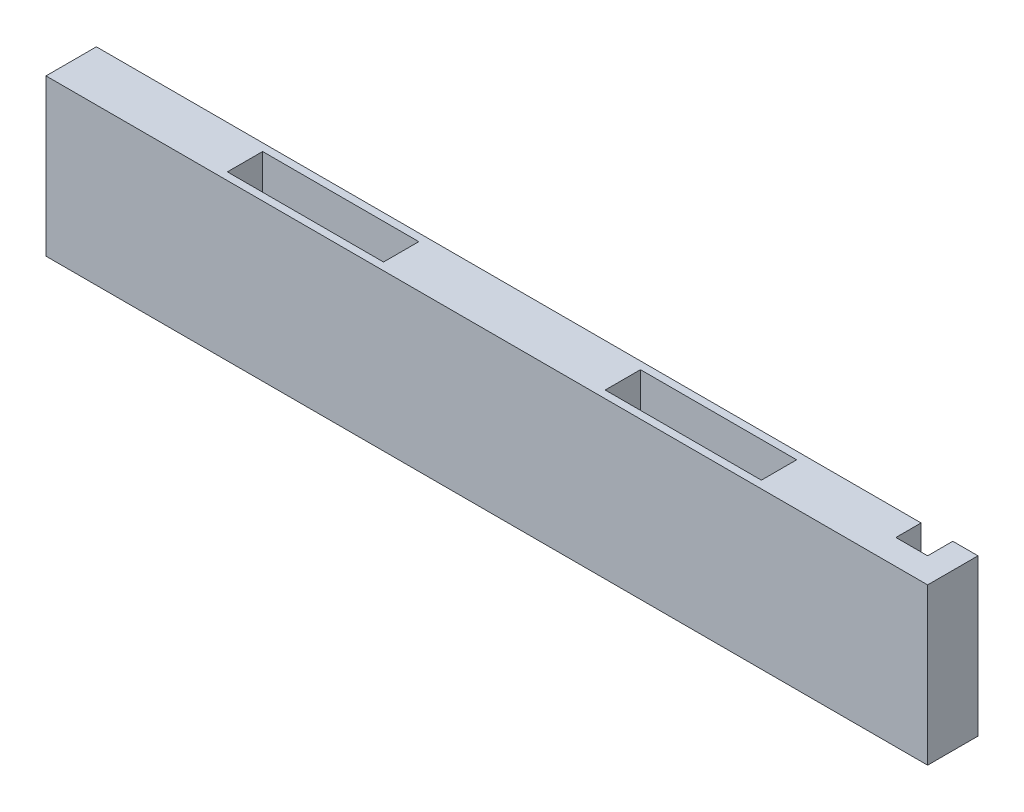
SolidWorks part; units mm, degrees
material "ABS"
ref_plane "Plano frontal" through (0, 0, 0) normal (0, 0, 1) x (1, 0, 0)
ref_plane "Plano superior" through (0, 0, 0) normal (0, 1, 0) x (1, 0, 0)
ref_plane "Plano direito" through (0, 0, 0) normal (1, 0, 0) x (0, 0, -1)
sketch "Esboço1" plane through (0, 0, 0) normal (0, 0, 1) x (1, 0, 0)
  line L1 (87.5, -15.5) -> (-87.5, -15.5)
  line L2 (87.5, -15.5) -> (87.5, 15.5)
  line L3 (87.5, 15.5) -> (-87.5, 15.5)
  line L4 (-87.5, -15.5) -> (-87.5, 15.5)
  line L5 (87.5, -15.5) -> (-87.5, 15.5) construction
  line L6 (87.5, 15.5) -> (-87.5, -15.5) construction
  point P0 (0, 0)
  dimension "D1" = 175
  dimension "D2" = 31
extrude "Ressalto-extrusão1" add sketch "Esboço1" along normal blind 10
sketch "Esboço2" plane through (0, 15.5, 0) normal (0, 1, 0) x (1, 0, 0)
  line L0 (-111.1236, -5) -> (103.3487, -5) construction
  line L1 (0, 16.6179) -> (0, -31.1724) construction
  line L2 (87.5, 0) -> (-87.5, 0) construction
  line L3 (-87.5, -10) -> (-87.5, 0) construction
  line L4 (-22, -8.5) -> (-53, -8.5)
  line L5 (-22, -8.5) -> (-22, -1.5)
  line L6 (-22, -1.5) -> (-53, -1.5)
  line L7 (-53, -8.5) -> (-53, -1.5)
  line L8 (-22, -8.5) -> (-53, -1.5) construction
  line L9 (-22, -1.5) -> (-53, -8.5) construction
  line L10 (22, -1.5) -> (53, -8.5) construction
  line L11 (22, -8.5) -> (53, -1.5) construction
  line L12 (53, -8.5) -> (53, -1.5)
  line L13 (22, -1.5) -> (53, -1.5)
  line L14 (22, -8.5) -> (22, -1.5)
  line L15 (22, -8.5) -> (53, -8.5)
  point P7 (-37.5, -5)
  point P21 (37.5, -5)
  dimension "D1" = 5
  dimension "D2" = 7
  dimension "D3" = 31
  dimension "D4" = 50
extrude "Corte-extrusão1" cut sketch "Esboço2" against normal blind 10.5
sketch "Esboço3" plane through (0, -15.5, 0) normal (0, -1, 0) x (1, 0, 0)
  line L0 (-105.0554, 5) -> (100.316, 5) construction
  line L1 (-87.5, 10) -> (87.5, 10) construction
  line L2 (0, 21.6875) -> (0, -29.1463) construction
  line L3 (-87.5, 10) -> (-87.5, 0) construction
  line L4 (-22, 1.5) -> (-53, 1.5)
  line L5 (-22, 1.5) -> (-22, 8.5)
  line L6 (-22, 8.5) -> (-53, 8.5)
  line L7 (-53, 1.5) -> (-53, 8.5)
  line L8 (-22, 1.5) -> (-53, 8.5) construction
  line L9 (-22, 8.5) -> (-53, 1.5) construction
  line L10 (22, 8.5) -> (53, 1.5) construction
  line L11 (22, 1.5) -> (53, 8.5) construction
  line L12 (53, 1.5) -> (53, 8.5)
  line L13 (22, 8.5) -> (53, 8.5)
  line L14 (22, 1.5) -> (22, 8.5)
  line L15 (22, 1.5) -> (53, 1.5)
  point P6 (-37.5, 5)
  point P19 (37.5, 5)
  dimension "D1" = 5
  dimension "D2" = 7
  dimension "D3" = 31
  dimension "D4" = 50
extrude "Corte-extrusão2" cut sketch "Esboço3" against normal blind 10.5
sketch "Esboço6" plane through (0, 0, 0) normal (0, 0, -1) x (-1, 0, 0)
  line L0 (-105.7639, 0) -> (108.9191, 0) construction
  line L1 (-87.5, 15.5) -> (87.5, 15.5) construction
  line L2 (-76.2, -15.5) -> (-82.5, -15.5)
  line L3 (-76.2, -15.5) -> (-76.2, 15.5)
  line L4 (-76.2, 15.5) -> (-82.5, 15.5)
  line L5 (-82.5, -15.5) -> (-82.5, 15.5)
  line L6 (-76.2, -15.5) -> (-82.5, 15.5) construction
  line L7 (-76.2, 15.5) -> (-82.5, -15.5) construction
  line L8 (-87.5, -15.5) -> (-87.5, 15.5) construction
  point P2 (-79.35, 0)
  dimension "D1" = 6.3
  dimension "D2" = 5
extrude "Corte-extrusão5" cut sketch "Esboço6" against normal blind 5
sketch "Esboço5" plane through (-87.5, 0, 0) normal (-1, 0, 0) x (0, 0, 1)
  line L0 (5, 26.6629) -> (5, -26.0741) construction
  line L1 (10, 15.5) -> (10, -15.5) construction
  line L2 (10, 15.5) -> (0, 15.5) construction
  line L3 (27.0388, 0) -> (-12.2765, 0) construction
  circle A0 centre (5, 10.5) radius 1.5
  circle A1 centre (5, -10.5) radius 1.5
  dimension "D2" = 3
  dimension "D1" = 5
  dimension "D3" = 5
extrude "Corte-extrusão4" cut sketch "Esboço5" against normal blind 8
sketch "Esboço4" plane through (-87.5, 0, 0) normal (-1, 0, 0) x (0, 0, 1)
  line L0 (-6.6733, 0) -> (16.3425, 0) construction
  line L1 (5, 27.5383) -> (5, -31.0406) construction
  line L2 (0, 15.5) -> (0, -15.5) construction
  line L3 (0, 2.5) -> (7.1407, -2.5)
  line L6 (0, -2.5) -> (7.1407, -2.5)
  line L7 (0, 2.5) -> (0, -2.5)
  point P12 (3.5704, 0)
  dimension "D1" = 5
  dimension "D2" = 5
  dimension "D3" = 55
extrude "Corte-extrusão6" cut sketch "Esboço4" against normal up to surface (163.7 mm away) up to face at (76.2, 0, 2.5)
